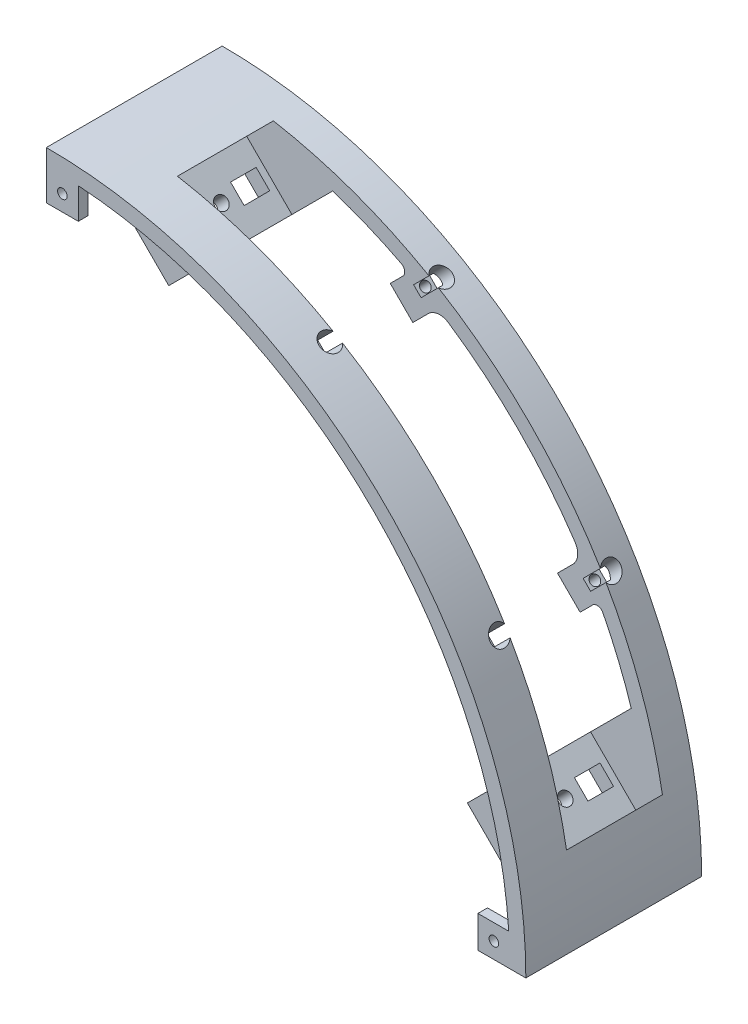
SolidWorks part; units mm, degrees
ref_plane "Plan de face" through (0, 0, 0) normal (0, 0, 1) x (1, 0, 0)
ref_plane "Plan de dessus" through (0, 0, 0) normal (0, 1, 0) x (1, 0, 0)
ref_plane "Plan de droite" through (0, 0, 0) normal (1, 0, 0) x (0, 0, -1)
sketch "Esquisse1" plane through (0, 0, 0) normal (0, 0, 1) x (1, 0, 0)
  line L0 (0, 0) -> (363.0166, 0) construction
  line L1 (0, 0) -> (0, 224.4802) construction
  line L2 (0, 150) -> (0, 145)
  line L3 (145, 0) -> (150, 0)
  arc A0 (0, 150) -> (150, 0) centre (0, 0) cw
  arc A1 (0, 145) -> (145, 0) centre (0, 0) cw
  dimension "D1" = 150
  dimension "D2" = 145
extrude "paroi" add sketch "Esquisse1" along normal blind 55
sketch "Esquisse11" plane through (0, 0, 0) normal (0, 0, -1) x (-1, 0, 0)
  line L1 (-145, 0) -> (-135, 0)
  line L2 (-145, 0) -> (-145, 10)
  line L3 (-145, 10) -> (-135, 10)
  line L4 (-135, 0) -> (-135, 10)
  line L5 (0, 145) -> (-10, 145)
  line L6 (0, 145) -> (0, 135)
  line L7 (0, 135) -> (-10, 135)
  line L8 (-10, 145) -> (-10, 135)
  dimension "D1" = 10
  dimension "D2" = 10
  dimension "D3" = 10
  dimension "D4" = 10
extrude "fixation_paroi_base" add sketch "Esquisse11" against normal blind 3
sketch "Esquisse13" plane through (0, 0, 3) normal (0, 0, 1) x (1, 0, 0)
  line L0 (10, 144.6548) -> (10, 135) construction
  line L1 (10, 135) -> (0, 135) construction
  line L2 (145, 0) -> (135, 0) construction
  line L3 (135, 0) -> (135, 10) construction
  circle A0 centre (5, 140) radius 1.5
  circle A1 centre (140, 5) radius 1.5
  dimension "D1" = 5
  dimension "D2" = 5
  dimension "D3" = 5
  dimension "D4" = 5
extrude "trou_fixation_paroi_base" cut sketch "Esquisse13" against normal through all
ref_plane "Plan1" through (75, 75, 0) normal (-0.7071, -0.7071, 0) x (-0.7071, 0.7071, 0)
sketch "Esquisse14" plane through (75, 75, 0) normal (-0.7071, -0.7071, 0) x (-0.7071, 0.7071, 0)
  line L0 (95.2153, 0) -> (-95.2153, 0) construction
  line L1 (86.066, -40) -> (-86.066, -40)
  line L2 (86.066, -40) -> (86.066, -10)
  line L3 (86.066, -10) -> (-86.066, -10)
  line L4 (-86.066, -40) -> (-86.066, -10)
  line L5 (-106.066, -55) -> (-106.066, 0) construction
  line L6 (106.066, -55) -> (106.066, 0) construction
  dimension "D1" = 30
  dimension "D2" = 10
  dimension "D3" = 20
  dimension "D4" = 20
extrude "extrusion bumper" cut sketch "Esquisse14" against normal up to next
sketch "Esquisse15" plane through (75, 75, 0) normal (-0.7071, -0.7071, 0) x (-0.7071, 0.7071, 0)
  line L1 (86.066, -40) -> (66.066, -40)
  line L2 (86.066, -40) -> (86.066, -45)
  line L3 (86.066, -45) -> (66.066, -45)
  line L4 (66.066, -40) -> (66.066, -45)
  line L5 (-86.066, -40) -> (-66.066, -40)
  line L6 (-86.066, -40) -> (-86.066, -45)
  line L7 (-86.066, -45) -> (-66.066, -45)
  line L8 (-66.066, -40) -> (-66.066, -45)
  line L9 (86.066, -10) -> (66.066, -10)
  line L10 (86.066, -10) -> (86.066, -5)
  line L11 (86.066, -5) -> (66.066, -5)
  line L12 (66.066, -10) -> (66.066, -5)
  line L13 (-86.066, -10) -> (-66.066, -10)
  line L14 (-86.066, -10) -> (-86.066, -5)
  line L15 (-86.066, -5) -> (-66.066, -5)
  line L16 (-66.066, -10) -> (-66.066, -5)
  dimension "D1" = 5
  dimension "D2" = 5
  dimension "D3" = 5
  dimension "D4" = 5
  dimension "D5" = 20
  dimension "D6" = 20
  dimension "D7" = 20
  dimension "D8" = 20
extrude "Boss.-Extru.1" add sketch "Esquisse15" against normal up to next
sketch "Esquisse16" plane through (0, 0, 45) normal (0, 0, 1) x (1, 0, 0)
  line L0 (135.8579, 14.1421) -> (121.7157, 28.2843)
  line L1 (121.7157, 28.2843) -> (125.2513, 31.8198)
  line L2 (137.9853, 44.5539) -> (121.7157, 28.2843) construction
  line L3 (125.2513, 31.8198) -> (139.3934, 17.6777)
  line L4 (143.3734, 21.6577) -> (135.8579, 14.1421) construction
  line L5 (139.3934, 17.6777) -> (135.8579, 14.1421)
  line L6 (28.2843, 121.7157) -> (14.1421, 135.8579)
  line L7 (14.1421, 135.8579) -> (17.6777, 139.3934)
  line L8 (21.6577, 143.3734) -> (14.1421, 135.8579) construction
  line L9 (17.6777, 139.3934) -> (31.8198, 125.2513)
  line L10 (44.5539, 137.9853) -> (28.2843, 121.7157) construction
  line L11 (31.8198, 125.2513) -> (28.2843, 121.7157)
  dimension "D1" = 5
  dimension "D2" = 5
extrude "Boss.-Extru.2" add sketch "Esquisse16" against normal up to surface (35 mm away) up to face at (85.1767, 85.1767, 10)
sketch "Esquisse17" plane through (75, 75, 0) normal (-0.7071, -0.7071, 0) x (-0.7071, 0.7071, 0)
  line L0 (66.066, -45) -> (86.066, -45) construction
  line L1 (-66.066, -5) -> (-86.066, -5) construction
  line L2 (66.066, -5) -> (66.066, -45) construction
  line L3 (-86.066, -5) -> (-86.066, -45) construction
  circle A0 centre (76.066, -25) radius 2
  circle A3 centre (-76.066, -25) radius 2
  dimension "D1" = 20
  dimension "D4" = 20
  dimension "D5" = 10
  dimension "D8" = 10
extrude "Enlèv. mat.-Extru.1" cut sketch "Esquisse17" against normal up to next
sketch "Esquisse18" plane through (0, 0, 55) normal (0, 0, 1) x (1, 0, 0)
  line L1 (0, 145) -> (10, 145)
  line L2 (0, 145) -> (0, 135)
  line L3 (0, 135) -> (10, 135)
  line L4 (10, 145) -> (10, 135)
  line L5 (145, 0) -> (135, 0)
  line L6 (145, 0) -> (145, 10)
  line L7 (145, 10) -> (135, 10)
  line L8 (135, 0) -> (135, 10)
  circle A0 centre (5, 140) radius 1.5
  circle A1 centre (140, 5) radius 1.5
  dimension "D5" = 5
  dimension "D1" = 10
  dimension "D2" = 10
  dimension "D3" = 10
  dimension "D4" = 10
  dimension "D6" = 5
  dimension "D7" = 5
  dimension "D8" = 5
extrude "Boss.-Extru.3" add sketch "Esquisse18" against normal blind 3
sketch "Esquisse19" plane through (0, 0, 45) normal (0, 0, 1) x (1, 0, 0)
  line L0 (44.5539, 137.9853) -> (28.2843, 121.7157)
  line L1 (28.2843, 121.7157) -> (14.1421, 135.8579)
  line L2 (14.1421, 135.8579) -> (21.6577, 143.3734)
  line L3 (0, 0) -> (-128.7868, 128.7868) construction
  line L4 (-121.7157, -28.2843) -> (-135.8579, -14.1421)
  line L5 (-137.9853, -44.5539) -> (-121.7157, -28.2843)
  line L6 (-135.8579, -14.1421) -> (-143.3734, -21.6577)
  arc A0 (21.6577, 143.3734) -> (44.5539, 137.9853) centre (0, 0) cw
  arc A1 (44.5539, 137.9853) -> (21.6577, 143.3734) centre (0, 0) ccw construction
  arc A2 (-143.3734, -21.6577) -> (-137.9853, -44.5539) centre (0, 0) ccw
sketch "Esquisse20" plane through (75, 75, 0) normal (-0.7071, -0.7071, 0) x (-0.7071, 0.7071, 0)
  line L0 (66.066, -45) -> (86.066, -45) construction
  line L1 (81.066, -37) -> (71.066, -37)
  line L2 (81.066, -37) -> (81.066, -31)
  line L3 (81.066, -31) -> (71.066, -31)
  line L4 (71.066, -37) -> (71.066, -31)
  line L5 (79.066, -20) -> (73.066, -20)
  line L6 (79.066, -20) -> (79.066, -12)
  line L7 (79.066, -12) -> (73.066, -12)
  line L8 (73.066, -20) -> (73.066, -12)
  line L9 (-71.066, -37) -> (-81.066, -37)
  line L10 (-71.066, -37) -> (-71.066, -31)
  line L11 (-71.066, -31) -> (-81.066, -31)
  line L12 (-81.066, -37) -> (-81.066, -31)
  line L13 (-73.066, -20) -> (-79.066, -20)
  line L14 (-73.066, -20) -> (-73.066, -12)
  line L15 (-73.066, -12) -> (-79.066, -12)
  line L16 (-79.066, -20) -> (-79.066, -12)
  line L17 (66.066, -5) -> (66.066, -45) construction
  line L18 (-86.066, -45) -> (-66.066, -45) construction
  line L19 (-66.066, -45) -> (-66.066, -5) construction
  line L20 (-66.066, -5) -> (-86.066, -5) construction
  line L21 (86.066, -5) -> (66.066, -5) construction
  dimension "D1" = 10
  dimension "D2" = 6
  dimension "D3" = 10
  dimension "D4" = 6
  dimension "D5" = 8
  dimension "D6" = 5
  dimension "D7" = 8
  dimension "D8" = 5
  dimension "D9" = 8
  dimension "D10" = 8
  dimension "D11" = 6
  dimension "D12" = 6
  dimension "D13" = 7
  dimension "D14" = 7
  dimension "D15" = 7
  dimension "D16" = 7
extrude "Enlèv. mat.-Extru.2" cut sketch "Esquisse20" against normal through all
sketch "Esquisse21" plane through (0, 0, 45) normal (0, 0, 1) x (1, 0, 0)
  line L0 (0, 0) -> (136.3904, 136.3904) construction
  line L1 (71.4178, 130.8148) -> (130.8148, 71.4178) construction
  line L2 (130.8148, 71.4178) -> (121.9759, 62.579) construction
  line L3 (121.9759, 62.579) -> (62.579, 121.9759) construction
  line L4 (62.579, 121.9759) -> (71.4178, 130.8148) construction
  line L5 (71.4178, 130.8148) -> (78.4889, 123.7437)
  line L6 (78.4889, 123.7437) -> (69.65, 114.9049)
  line L7 (69.65, 114.9049) -> (62.579, 121.9759)
  line L8 (62.579, 121.9759) -> (71.4178, 130.8148)
  line L9 (130.8148, 71.4178) -> (123.7437, 78.4889)
  line L10 (123.7437, 78.4889) -> (114.9049, 69.65)
  line L11 (114.9049, 69.65) -> (121.9759, 62.579)
  line L12 (121.9759, 62.579) -> (130.8148, 71.4178)
  dimension "D1" = 12.5
  dimension "D2" = 143
  dimension "D3" = 84
  dimension "D4" = 42
  dimension "D5" = 10
  dimension "D6" = 10
extrude "Boss.-Extru.4" add sketch "Esquisse21" against normal blind 5
sketch "Esquisse24" plane through (0, 0, 10) normal (0, 0, 1) x (1, 0, 0)
  line L0 (0, 0) -> (137.9242, 137.9242) construction
  line L1 (62.579, 121.9759) -> (121.9759, 62.579) construction
  line L2 (121.9759, 62.579) -> (130.4628, 71.0659) construction
  line L3 (130.4628, 71.0659) -> (71.0659, 130.4628) construction
  line L4 (71.0659, 130.4628) -> (62.579, 121.9759) construction
  line L5 (62.579, 121.9759) -> (71.0659, 130.4628)
  line L6 (71.0659, 130.4628) -> (78.1369, 123.3918)
  line L7 (78.1369, 123.3918) -> (69.65, 114.9049)
  line L8 (69.65, 114.9049) -> (62.579, 121.9759)
  line L9 (121.9759, 62.579) -> (130.4628, 71.0659)
  line L10 (130.4628, 71.0659) -> (123.3918, 78.1369)
  line L11 (123.3918, 78.1369) -> (114.9049, 69.65)
  line L12 (114.9049, 69.65) -> (121.9759, 62.579)
  dimension "D1" = 10
  dimension "D2" = 10
extrude "Boss.-Extru.5" add sketch "Esquisse24" against normal blind 5
sketch "Esquisse25" plane through (92.2774, 92.2774, 0) normal (-0.7071, -0.7071, 0) x (0, 0, 1)
  line L0 (45, 42) -> (45, 32) construction
  line L1 (42.5, 37.5) -> (7.5, 37.5) construction
  line L2 (42.5, 37.5) -> (42.5, -37.5) construction
  line L3 (42.5, -37.5) -> (7.5, -37.5) construction
  line L4 (7.5, 37.5) -> (7.5, -37.5) construction
  line L6 (5, 42) -> (10, 42) construction
  line L7 (45, -42) -> (40, -42) construction
  circle A0 centre (42.5, 37.5) radius 1.5
  circle A1 centre (42.5, -37.5) radius 1.5
  circle A2 centre (7.5, 37.5) radius 1.5
  circle A3 centre (7.5, -37.5) radius 1.5
  dimension "D1" = 2.5
  dimension "D2" = 35
  dimension "D3" = 4.5
  dimension "D4" = 4.5
extrude "Enlèv. mat.-Extru.3" cut sketch "Esquisse25" against normal up to next
sketch "Esquisse26" plane through (0, 0, 55) normal (0, 0, 1) x (1, 0, 0)
  line L0 (140.7661, 0) -> (-9.2339, 0) construction
  line L1 (0, -9.6191) -> (0, 140.3809) construction
  line L2 (212.132, 0) -> (0, 212.132) construction
  line L3 (135, 0) -> (150, 0) construction
  line L4 (0, 150) -> (0, 135) construction
  dimension "D1" = 150
  dimension "D2" = 0
  dimension "D3" = 0
  dimension "D4" = 135
sketch "Esquisse28" plane through (75, 75, 0) normal (-0.7071, -0.7071, 0) x (-0.7071, 0.7071, 0)
  line L0 (106.066, 0) -> (182.3978, 0) construction
sketch "Esquisse30" plane through (92.2774, 92.2774, 0) normal (-0.7071, -0.7071, 0) x (-0.7071, 0.7071, 0)
  line L1 (37.5, -42.5) -> (-37.5, -42.5) construction
  line L2 (37.5, -42.5) -> (37.5, -7.5) construction
  line L3 (37.5, -7.5) -> (-37.5, -7.5) construction
  line L4 (-37.5, -42.5) -> (-37.5, -7.5) construction
  dimension "D1" = 75
  dimension "D2" = 35
sketch "Esquisse34" plane through (0, 0, 0) normal (-1, 0, 0) x (0, 0, 1)
  line L0 (55, 212.132) -> (0, 212.132) construction
  line L1 (55, 0) -> (55, 212.132) construction
  line L2 (0, -141271.3562) -> (0, 141625.331) construction
ref_plane "Plan3" through (106.066, 106.066, 0) normal (-0.7071, -0.7071, 0) x (0, 0, 1)
sketch "Esquisse35" plane through (106.066, 106.066, 0) normal (-0.7071, -0.7071, 0) x (0, 0, 1)
  line L0 (42.5, 37.5) -> (42.5, -37.5) construction
  line L1 (42.5, -37.5) -> (7.5, -37.5) construction
  line L2 (42.5, -37.5) -> (42.5, 37.5) construction
  line L3 (42.5, 37.5) -> (7.5, 37.5) construction
  line L4 (7.5, -37.5) -> (7.5, 37.5) construction
  line L5 (42.5, 37.5) -> (7.5, 37.5) construction
  circle A0 centre (42.5, -37.5) radius 3
  circle A1 centre (42.5, 37.5) radius 3
  circle A2 centre (7.5, -37.5) radius 3
  circle A3 centre (7.5, 37.5) radius 3
  dimension "D1" = 35
  dimension "D2" = 75
  dimension "D3" = 0
  dimension "D4" = 0
extrude "Enlèv. mat.-Extru.4" cut sketch "Esquisse35" along normal blind 12
fillet "Congé1" radius 5 4 edges at (122.6299, 77.3751, 7.5) (122.6299, 77.3751, 42.5) (77.3751, 122.6299, 7.5) (77.3751, 122.6299, 42.5)
fillet "Congé2" radius 2 4 edges at (68.4366, 127.8336, 42.5) (68.4366, 127.8336, 7.5) (127.8336, 68.4366, 7.5) (127.8336, 68.4366, 42.5)
